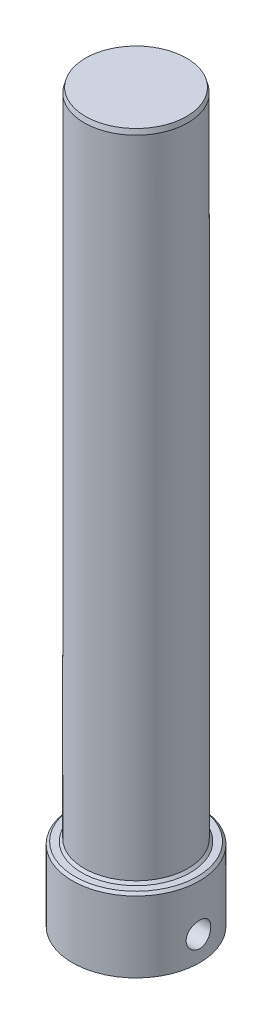
SolidWorks part; units mm, degrees
material "6061-T6 (SS)"
ref_plane "Front Plane" through (0, 0, 0) normal (0, 0, 1) x (1, 0, 0)
ref_plane "Top Plane" through (0, 0, 0) normal (0, 1, 0) x (1, 0, 0)
ref_plane "Right Plane" through (0, 0, 0) normal (1, 0, 0) x (0, 0, -1)
sketch "Sketch1" plane through (0, 0, 0) normal (0, 1, 0) x (1, 0, 0)
  circle A0 centre (0, 0) radius 16.51
  dimension "D1" = 33.02
extrude "Boss-Extrude1" add sketch "Sketch1" against normal blind 19.05
sketch "Sketch2" plane through (0, 0, 0) normal (0, 1, 0) x (-1, 0, 0)
  circle A0 centre (0, 0) radius 13.462
  dimension "D1" = 26.924
extrude "Boss-Extrude2" add sketch "Sketch2" along normal blind 169.545
sketch "Sketch3" plane through (0, -19.05, 0) normal (0, -1, 0) x (1, 0, 0)
  circle A0 centre (0, 0) radius 10.2
  dimension "D1" = 20.4
extrude "Cut-Extrude1" cut sketch "Sketch3" against normal blind 15.875
sketch "Sketch4" plane through (0, -3.175, 0) normal (0, -1, 0) x (1, 0, 0)
  circle A0 centre (0, 0) radius 6.35
hole_wizard "M6 Clearance Hole1" positions "3DSketch1" profile "Sketch5" hole size "M6" standard "ANSI Metric"
sketch3d "3DSketch1"
  line L0 (0, 0, 0) -> (0, -12.675, 0) construction
  line L1 (0, -12.675, 0) -> (-16.51, -12.675, 0) construction
  point P0 (-16.51, -12.675, 0)
  dimension "D1" = 9.5
sketch "Sketch5" plane through (-16.51, -12.675, 0) normal (0, 1, 0) x (0, 0, 1)
  line L0 (0, 0) -> (0, 6.31)
  line L1 (0, 6.31) -> (3.2004, 6.31)
  line L2 (3.2004, 6.31) -> (3.2004, 0)
  line L5 (3.2004, 0) -> (0, 0)
  line L11 (0, -6.35) -> (0, 107.95) construction
  dimension "Thru Hole Dia." = 6.4008
  dimension "Thru Hole Depth" = 6.31
ref_plane "Plane1" through (9.5089, 0, 0) normal (-1, 0, 0) x (0, 0, 1)
hole_wizard "M6 Clearance Hole2" positions "Sketch7" profile "Sketch6" hole size "M6" standard "ANSI Metric"
sketch "Sketch7" plane through (9.5089, 0, 0) normal (-1, 0, 0) x (0, 0, 1)
  line L0 (0, 0) -> (0, -12.675) construction
  point P0 (0, -12.675)
sketch "Sketch6" plane through (9.5089, -12.675, 0) normal (0, 1, 0) x (0, 0, 1)
  line L0 (0, 0) -> (0, 7.0011)
  line L1 (0, 7.0011) -> (3.2004, 7.0011)
  line L2 (3.2004, 7.0011) -> (3.2004, 0)
  line L5 (3.2004, 0) -> (0, 0)
  line L11 (0, -6.35) -> (0, 107.95) construction
  dimension "Thru Hole Dia." = 6.4008
  dimension "Thru Hole Depth" = 7.0011
chamfer "Chamfer1" [suppressed] distance 1.27 angle 45
chamfer "Chamfer2" distance 1.27 angle 45 1 edges at (0, -19.05, 10.2)
chamfer "Chamfer3" distance 0.635 angle 45 1 edges at (0, 0, -16.51)
chamfer "Chamfer4" distance 0.635 angle 45 1 edges at (0, 0, 13.462)
chamfer "Chamfer5" distance 0.3403 angle 75 1 edges at (0, 169.545, 13.462)
sketch "Sketch10" [suppressed] plane through (0, -3.175, 0) normal (0, -1, 0) x (1, 0, 0)
  circle A0 centre (0, 0) radius 6.35
  dimension "D1" = 12.7
hole_wizard "25/32 (0.78125) Diameter Hole1" positions "Sketch8" profile "Sketch9" hole size "25/32" standard "ANSI Inch"
sketch "Sketch8" plane through (0, -3.175, 0) normal (0, -1, 0) x (-1, 0, 0)
  point P0 (0, 0)
sketch "Sketch9" plane through (0, -3.175, 0) normal (1, 0, 0) x (0, 0, -1)
  line L0 (0, 0) -> (0, 166.37)
  line L1 (0, 166.37) -> (9.9219, 160.4083)
  line L2 (9.9219, 160.4083) -> (9.9219, 0)
  line L5 (9.9219, 0) -> (0, 0)
  line L10 (0, 166.37) -> (-9.9219, 160.4083) construction
  line L11 (0, -6.35) -> (0, 107.95) construction
  dimension "Hole Dia." = 19.8438
  dimension "Hole Depth" = 166.37
  dimension "Drill Angle" = 118
